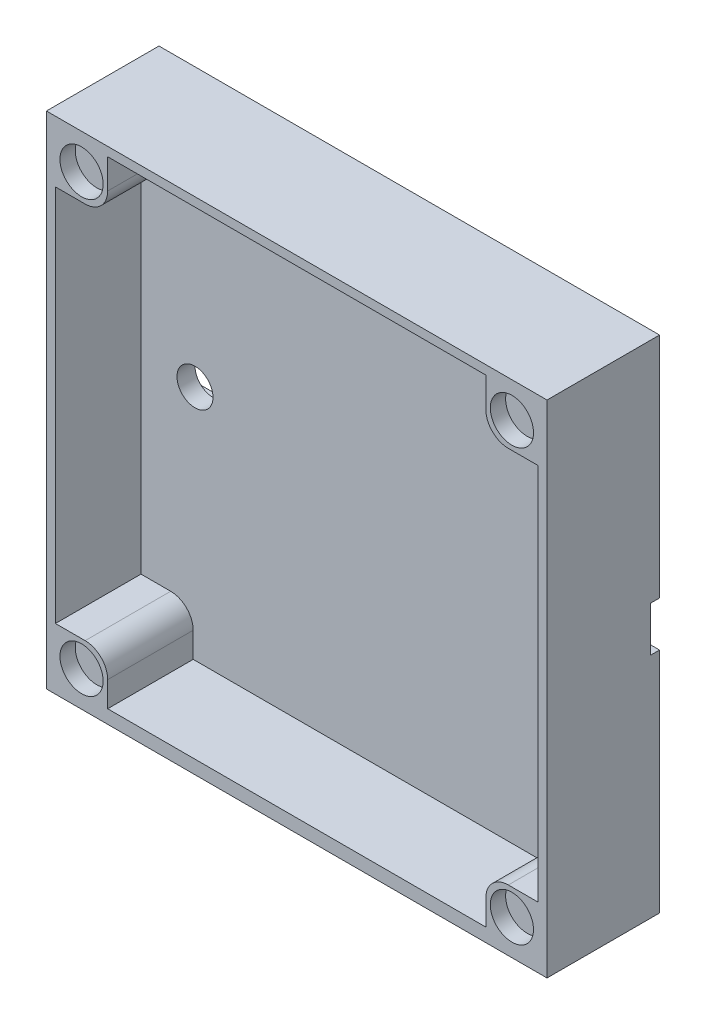
SolidWorks part; units mm, degrees
ref_plane "Přední rovina" through (0, 0, 0) normal (0, 0, 1) x (1, 0, 0)
ref_plane "Horní rovina" through (0, 0, 0) normal (0, 1, 0) x (1, 0, 0)
ref_plane "Pravá rovina" through (0, 0, 0) normal (1, 0, 0) x (0, 0, -1)
sketch "Skica1" plane through (0, 0, 0) normal (0, 0, 1) x (1, 0, 0)
  line L1 (27.8, 27.8) -> (-27.8, 27.8)
  line L2 (27.8, 27.8) -> (27.8, -27.8)
  line L3 (27.8, -27.8) -> (-27.8, -27.8)
  line L4 (-27.8, 27.8) -> (-27.8, -27.8)
  line L5 (27.8, 27.8) -> (-27.8, -27.8) construction
  line L6 (27.8, -27.8) -> (-27.8, 27.8) construction
  point P0 (0, 0)
  point P5 (-27.5, 0)
  point P11 (4.5, 0)
  dimension "D1" = 55.6
  dimension "D2" = 55.6
extrude "Přidat vysunutím2" add sketch "Skica1" along normal blind 3 contours L2 L1 L4 L3
sketch "Skica5" plane through (0, 0, 0) normal (0, 0, -1) x (-1, 0, 0)
  line L10 (27.8, 27.8) -> (27.8, -27.8) construction
  line L11 (-27.8, 2.5) -> (27.8, 2.5)
  line L12 (-27.8, 2.5) -> (-27.8, -2.5)
  line L13 (-27.8, -2.5) -> (27.8, -2.5)
  line L14 (27.8, 2.5) -> (27.8, -2.5)
  line L15 (-27.8, 2.5) -> (27.8, -2.5) construction
  line L16 (-27.8, -2.5) -> (27.8, 2.5) construction
  point P0 (0, 0)
  dimension "D1" = 5
extrude "Odebrat vysunutím3" cut sketch "Skica5" against normal blind 1 contours L11 L14 L13 L12
sketch "Skica14" plane through (0, 0, 3) normal (0, 0, 1) x (1, 0, 0)
  line L1 (-27.8, 27.8) -> (27.8, 27.8)
  line L2 (-27.8, 27.8) -> (-27.8, -27.8)
  line L3 (-27.8, -27.8) -> (27.8, -27.8)
  line L4 (27.8, 27.8) -> (27.8, -27.8)
  line L5 (-26.8, 26.8) -> (26.8, 26.8)
  line L6 (-26.8, 26.8) -> (-26.8, -27.8)
  line L7 (-26.8, -27.8) -> (26.8, -27.8)
  line L8 (26.8, 26.8) -> (26.8, -27.8)
  line L9 (-26.8, -27.8) -> (26.8, -27.8)
  line L10 (-26.8, -27.8) -> (-26.8, -26.8)
  line L12 (26.8, -27.8) -> (26.8, -26.3)
  line L13 (-26.8, -27.8) -> (26.8, -27.8)
  line L14 (-26.8, -27.8) -> (-26.8, -26.3)
  line L15 (-26.8, -26.3) -> (26.8, -26.3)
  line L16 (26.8, -27.8) -> (26.8, -26.3)
  line M13 (-27.8, -27.8) -> (27.8, -27.8)
  line M14 (27.8, -27.8) -> (27.8, 27.8)
  line M15 (27.8, 27.8) -> (-27.8, 27.8)
  line M16 (-27.8, 27.8) -> (-27.8, -27.8)
  dimension "D1" = 1
  dimension "D2" = 1
  dimension "D3" = 1
  dimension "D4" = 0
  dimension "D5" = 1
  dimension "D6" = 53.6
extrude "Přidat vysunutím9" add sketch "Skica14" along normal blind 9.5 contours L5 L8 L6 M13 M14 M15 M16 | L14 L13 L16 L15
sketch "Skica17" plane through (0, 0, 1) normal (0, 0, -1) x (-1, 0, 0)
  line L0 (-27.8, 2.5) -> (-27.8, -2.5) construction
  line L1 (-12.5, -2.5) -> (-12.5, 2.5) construction
  line L2 (27.8, 2.5) -> (27.8, -2.5) construction
  circle A0 centre (-20.8, 0) radius 2
  circle A1 centre (20.8, 0) radius 2
  dimension "D1" = 4
  dimension "D2" = 4
  dimension "D3" = 7
  dimension "D4" = 8.3
  dimension "D5" = 7
extrude "Odebrat vysunutím8" cut sketch "Skica17" against normal blind 4
sketch "Skica19" plane through (0, 0, 0) normal (0, 0, -1) x (-1, 0, 0)
  line L1 (-27.8, 27.8) -> (-21, 27.8)
  line L2 (-27.8, 27.8) -> (-27.8, 21)
  line L3 (-27.8, 21) -> (-21, 21)
  line L4 (-21, 27.8) -> (-21, 21)
  line L5 (27.8, 27.8) -> (21, 27.8)
  line L6 (27.8, 27.8) -> (27.8, 21)
  line L7 (27.8, 21) -> (21, 21)
  line L8 (21, 27.8) -> (21, 21)
  line L9 (-27.8, -27.8) -> (-21, -27.8)
  line L10 (-27.8, -27.8) -> (-27.8, -21)
  line L11 (-27.8, -21) -> (-21, -21)
  line L12 (-21, -27.8) -> (-21, -21)
  line L13 (27.8, -27.8) -> (21, -27.8)
  line L14 (27.8, -27.8) -> (27.8, -21)
  line L15 (27.8, -21) -> (21, -21)
  line L16 (21, -27.8) -> (21, -21)
  dimension "D1" = 6.8
  dimension "D2" = 6.8
  dimension "D3" = 6.8
  dimension "D4" = 6.8
extrude "Přidat vysunutím10" add sketch "Skica19" against normal blind 12.5
sketch "Skica20" plane through (0, 0, 12.5) normal (0, 0, 1) x (1, 0, 0)
  line L0 (-27.8, -27.8) -> (27.8, -27.8) construction
  line L2 (-27.8, 27.8) -> (-27.8, -27.8) construction
  line L3 (27.8, 27.8) -> (-27.8, 27.8) construction
  line L4 (27.8, -27.8) -> (27.8, 27.8) construction
  line L5 (-27.8, -27.8) -> (27.8, -27.8) construction
  circle A0 centre (-23.9, -23.9) radius 2.4
  circle A1 centre (-23.9, 23.9) radius 2.4
  circle A2 centre (23.9003, 23.9) radius 2.4
  circle A3 centre (23.9003, -23.9) radius 2.4
  dimension "D1" = 4.8
  dimension "D4" = 4.8
  dimension "D5" = 3.9
  dimension "D7" = 4.8
  dimension "D10" = 4.8
  dimension "D2" = 3.9
  dimension "D3" = 3.9
  dimension "D6" = 3.9
  dimension "D8" = 3.8997
  dimension "D9" = 3.9
  dimension "D11" = 3.9
  dimension "D12" = 3.8997
extrude "Odebrat vysunutím9" cut sketch "Skica20" against normal blind 1.7
fillet "Zaoblit1" radius 2.5 4 edges at (21, 21, 7.75) (21, -21, 7.75) (-21, -21, 7.75) (-21, 21, 7.75)
